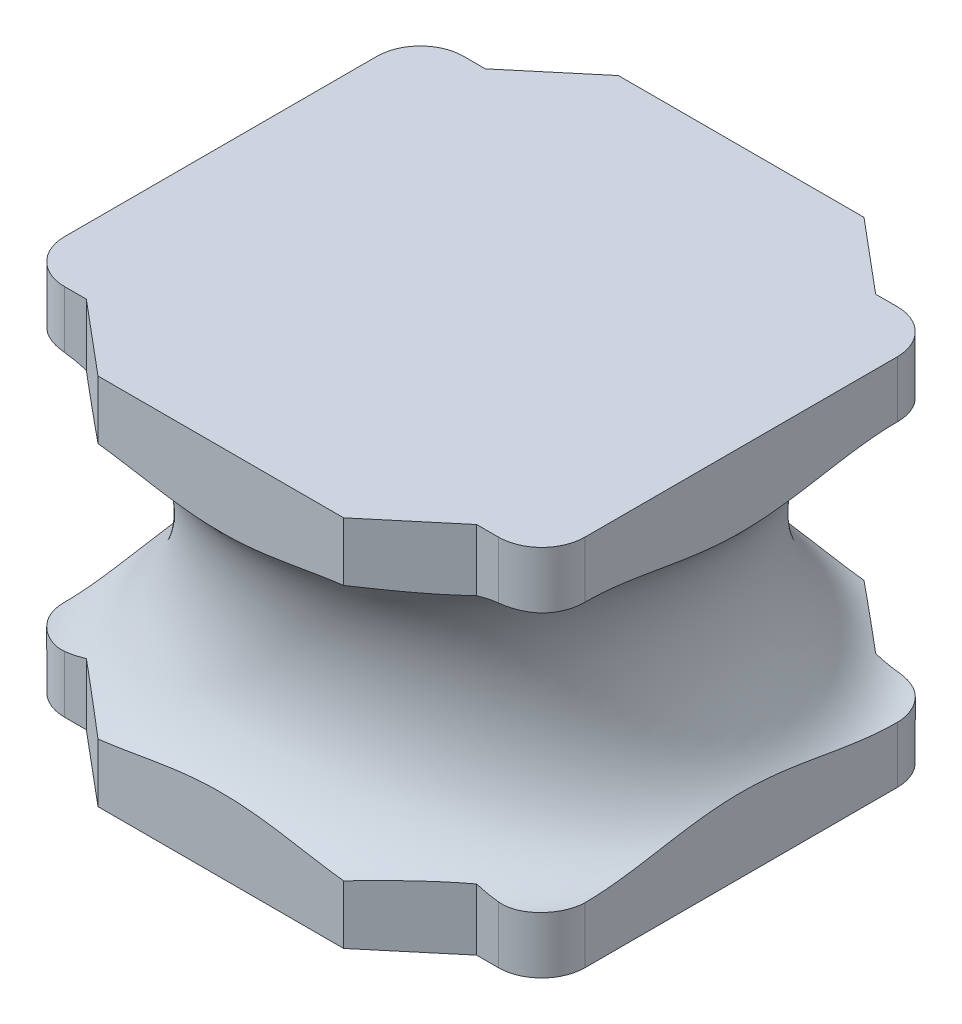
SolidWorks part; units mm, degrees
ref_plane "Front Plane" through (0, 0, 0) normal (0, 0, 1) x (1, 0, 0)
ref_plane "Top Plane" through (0, 0, 0) normal (0, 1, 0) x (1, 0, 0)
ref_plane "Right Plane" through (0, 0, 0) normal (1, 0, 0) x (0, 0, -1)
sketch "Sketch1" plane through (0, 0, 0) normal (0, 1, 0) x (1, 0, 0)
  line L0 (3, -3) -> (-3, 3) construction
  line L1 (-1.4158, -3) -> (1.4158, -3)
  line L2 (-3, -1.8) -> (-3, 1.8)
  line L3 (-1.4158, 3) -> (1.4158, 3)
  line L4 (3, -1.8) -> (3, 1.8)
  line L5 (-2.5, 2.3) -> (-2.25, 2.3)
  line L6 (-2.25, 2.3) -> (-1.4158, 3)
  line L7 (0, 0) -> (0, 3) construction
  line L8 (0, 0) -> (-1.5257, 0) construction
  line L9 (-3, 2.3) -> (-3, 3) construction
  line L10 (-3, 3) -> (-1.4158, 3) construction
  line L11 (2.25, 2.3) -> (1.4158, 3)
  line L12 (2.5, 2.3) -> (2.25, 2.3)
  line L13 (-2.5, -2.3) -> (-2.25, -2.3)
  line L14 (-2.25, -2.3) -> (-1.4158, -3)
  line L15 (2.25, -2.3) -> (1.4158, -3)
  line L16 (2.5, -2.3) -> (2.25, -2.3)
  arc A0 (-3, 1.8) -> (-2.5, 2.3) centre (-2.5, 1.8) cw
  arc A1 (3, 1.8) -> (2.5, 2.3) centre (2.5, 1.8) ccw
  arc A2 (-3, -1.8) -> (-2.5, -2.3) centre (-2.5, -1.8) ccw
  arc A3 (3, -1.8) -> (2.5, -2.3) centre (2.5, -1.8) cw
  dimension "D6" = 0.5
  dimension "D1" = 6
  dimension "D2" = 2.3
  dimension "D3" = 40
  dimension "D4" = 0.75
  dimension "D5" = 6
extrude "Boss-Extrude1" add sketch "Sketch1" along normal blind 4.3
sketch "Sketch2" plane through (0, 0, 0) normal (0, 0, 1) x (1, 0, 0)
  line L0 (0, 0) -> (0, 4.3) construction
  line L1 (-1.4158, 4.3) -> (1.4158, 4.3) construction
  line L2 (0, 2.15) -> (3.5, 2.15) construction
  line L3 (3.5, 0.65) -> (3.5, 3.65) construction
  ellipse E0 centre (3.5, 2.15) end of major axis (3.5, 3.65) minor radius 1
  dimension "D1" = 3
  dimension "D2" = 2
  dimension "D3" = 3.5
revolve "Cut-Revolve1" cut sketch "Sketch2" angle 360 about L0
